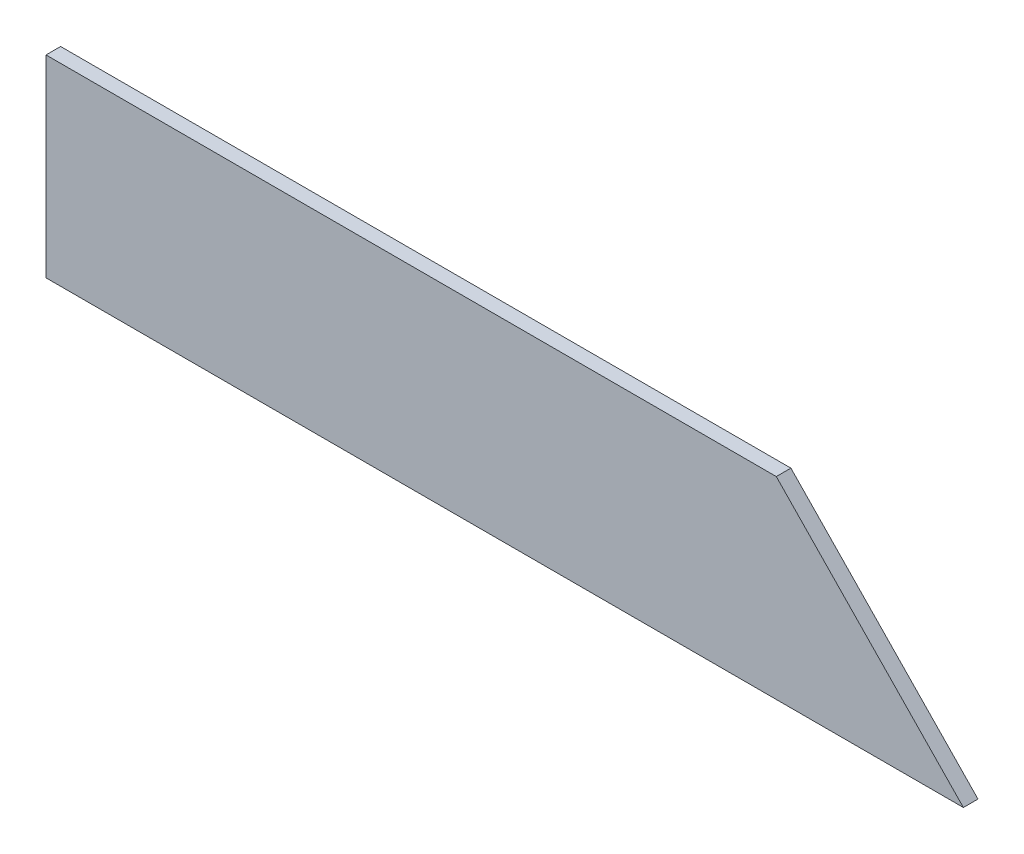
SolidWorks part; units mm, degrees
material "Pine"
ref_plane "Front Plane" through (0, 0, 0) normal (0, 0, 1) x (1, 0, 0)
ref_plane "Top Plane" through (0, 0, 0) normal (0, 1, 0) x (1, 0, 0)
ref_plane "Right Plane" through (0, 0, 0) normal (1, 0, 0) x (0, 0, -1)
sketch "Sketch1" plane through (0, 0, 0) normal (0, 0, 1) x (1, 0, 0)
  line L0 (625.3909, -12.2354) -> (391.555, 229.0646)
  line L1 (-521.1651, 229.0646) -> (391.555, 229.0646)
  line L2 (-521.1651, 229.0646) -> (-521.1651, -12.2354)
  line L3 (-521.1651, -12.2354) -> (625.3909, -12.2354)
  dimension "D1" = 1146.556
  dimension "D2" = 45.9
  dimension "D3" = 241.3
  dimension "D4" = 912.72
extrude "Boss-Extrude1" add sketch "Sketch1" along normal blind 18.2562
sketch "Sketch2" plane through (-521.1651, 0, 0) normal (-1, 0, 0) x (0, 0, 1)
  line L0 (0, -12.2354) -> (0, -30.0154) construction
  line L1 (0, -12.2354) -> (0, 46.6926)
  line L2 (0, 229.0646) -> (0, -12.2354) construction
  line L3 (0, 46.6926) -> (18.416, -30.0154)
  line L4 (0, -12.2354) -> (0, -30.0154)
  line L5 (0, -30.0154) -> (18.416, -30.0154)
  dimension "D1" = 17.78
  dimension "D2" = 58.928
  dimension "D3" = 13.5
extrude "Cut-Extrude1" [suppressed] cut sketch "Sketch2" against normal through all
chamfer "Chamfer1" [suppressed] distance 63.5 angle 15
